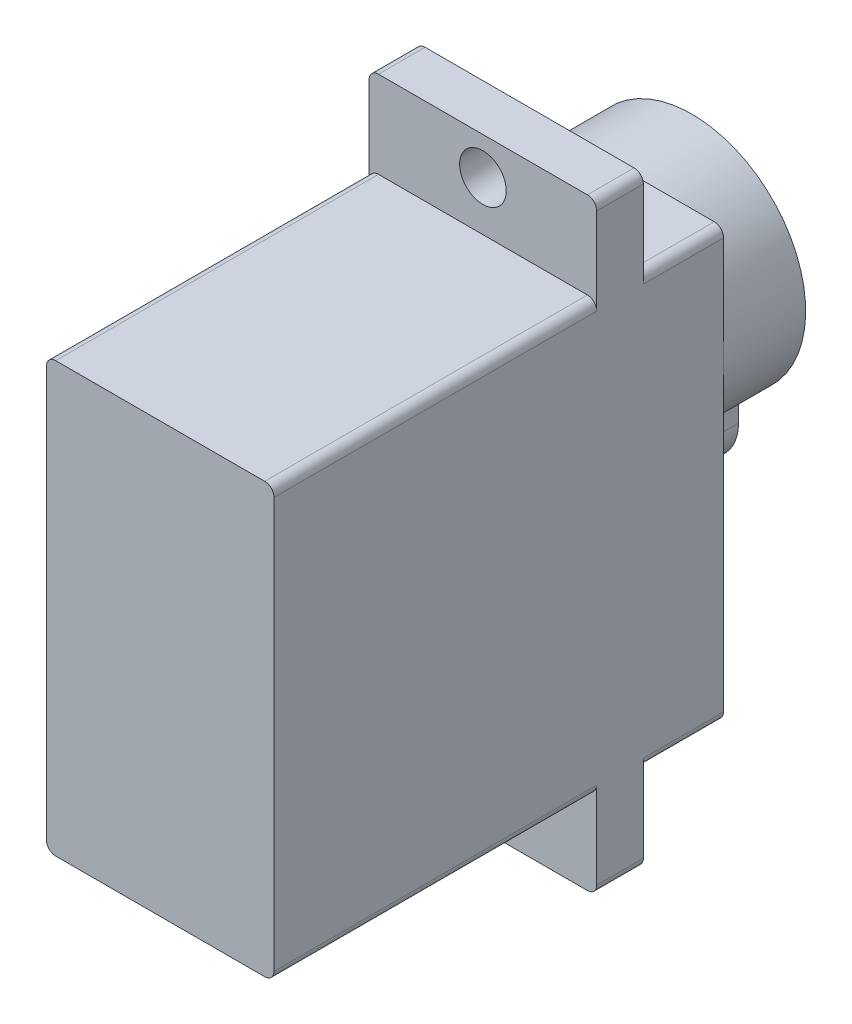
SolidWorks part; units mm, degrees
ref_plane "Ebene vorne" through (0, 0, 0) normal (0, 0, 1) x (1, 0, 0)
ref_plane "Ebene oben" through (0, 0, 0) normal (0, 1, 0) x (1, 0, 0)
ref_plane "Ebene rechts" through (0, 0, 0) normal (1, 0, 0) x (0, 0, -1)
sketch "Sketch1" plane through (0, 0, 0) normal (0, 0, 1) x (1, 0, 0)
  line L1 (-5.6, -11.5) -> (5.6, -11.5)
  line L2 (-6.1, -11) -> (-6.1, 11)
  line L3 (-5.6, 11.5) -> (5.6, 11.5)
  line L4 (6.1, -11) -> (6.1, 11)
  line L5 (-6.1, -11.5) -> (6.1, 11.5) construction
  line L6 (-6.1, 11.5) -> (6.1, -11.5) construction
  arc A0 (5.6, -11.5) -> (6.1, -11) centre (5.6, -11) ccw
  arc A1 (-6.1, 11) -> (-5.6, 11.5) centre (-5.6, 11) cw
  arc A2 (-5.6, -11.5) -> (-6.1, -11) centre (-5.6, -11) cw
  arc A3 (5.6, 11.5) -> (6.1, 11) centre (5.6, 11) cw
  point P0 (0, 0)
  dimension "D3" = 0.5
  dimension "D1" = 12.2
  dimension "D2" = 23
extrude "Boss-Extrude1" add sketch "Sketch1" along normal mid plane 24.1
ref_plane "Plane1" through (0, 0, -7.75) normal (0, 0, 1) x (1, 0, 0)
sketch "Sketch2" plane through (0, 0, -7.75) normal (0, 0, 1) x (1, 0, 0)
  line L0 (6.1, 11) -> (6.1, 15.65)
  line L1 (-6.1, 11) -> (-6.1, 15.65)
  line L3 (-5.6, 16.15) -> (5.6, 16.15)
  line L4 (5.6, 11.5) -> (-5.6, 11.5) construction
  line L5 (5.6, 11.5) -> (-5.6, 11.5)
  line L6 (8.608, 0) -> (-10.8961, 0) construction
  line L7 (5.6, -11.5) -> (-5.6, -11.5)
  line L8 (6.1, -11) -> (6.1, -15.65)
  line L9 (-5.6, -16.15) -> (5.6, -16.15)
  line L10 (-6.1, -11) -> (-6.1, -15.65)
  line L11 (0, 16.5614) -> (0, 11.1261) construction
  arc A0 (-5.6, 11.5) -> (-6.1, 11) centre (-5.6, 11) ccw construction
  arc A1 (6.1, 11) -> (5.6, 11.5) centre (5.6, 11) ccw construction
  arc A2 (-5.6, 11.5) -> (-6.1, 11) centre (-5.6, 11) ccw
  arc A3 (6.1, 11) -> (5.6, 11.5) centre (5.6, 11) ccw
  circle A4 centre (0, 14.15) radius 1.25
  circle A5 centre (0, -14.15) radius 1.25
  arc A6 (-5.6, -11.5) -> (-6.1, -11) centre (-5.6, -11) cw
  arc A7 (6.1, -11) -> (5.6, -11.5) centre (5.6, -11) cw
  arc A8 (-5.6, -16.15) -> (-6.1, -15.65) centre (-5.6, -15.65) cw
  arc A9 (6.1, -15.65) -> (5.6, -16.15) centre (5.6, -15.65) cw
  arc A10 (-6.1, 15.65) -> (-5.6, 16.15) centre (-5.6, 15.65) cw
  arc A11 (6.1, 15.65) -> (5.6, 16.15) centre (5.6, 15.65) ccw
  point P28 (-6.1, -16.15)
  point P31 (6.1, -16.15)
  point P34 (-6.1, 16.15)
  point P37 (6.1, 16.15)
  dimension "D1" = 2.5
  dimension "D4" = 0.5
  dimension "D2" = 2.65
  dimension "D3" = 32.3
extrude "Boss-Extrude2" add sketch "Sketch2" along normal blind 2.5
sketch "Sketch3" plane through (0, 0, -12.05) normal (0, 0, -1) x (-1, 0, 0)
  line L0 (-5.6, 11.5) -> (5.6, 11.5) construction
  line L1 (-2.5, -1.6) -> (-2.5, -0.1642)
  line L2 (2.5, -1.6) -> (2.5, -0.1642)
  arc A0 (2.5, -0.1642) -> (-2.5, -0.1642) centre (0, 5.4) ccw
  arc A1 (-2.5, -1.6) -> (2.5, -1.6) centre (0, -1.6) ccw
  dimension "D1" = 12.2
  dimension "D2" = 5
  dimension "D3" = 7
extrude "Boss-Extrude3" add sketch "Sketch3" along normal blind 4.4
sketch "Sketch4" plane through (0, 0, -16.45) normal (0, 0, -1) x (-1, 0, 0)
  circle A0 centre (0, 5.4) radius 0.5
  arc A1 (2.5, -0.1642) -> (-2.5, -0.1642) centre (0, 5.4) ccw construction
  dimension "D1" = 1
extrude "Boss-Extrude4" add sketch "Sketch4" along normal blind 3.7
chamfer "Chamfer1" distance 0.1 angle 45 1 edges at (-0.5, 5.4, -20.15)
sketch "Sketch5" plane through (-6.1, 0, 0) normal (-1, 0, 0) x (0, 0, 1)
  line L0 (-71.3637, 35.6636) -> (-71.3637, 299.6636) construction
ref_plane "Plane2" through (0, 0, 0) normal (-1, 0, 0) x (0, 0, 1)
sketch "Sketch7"
